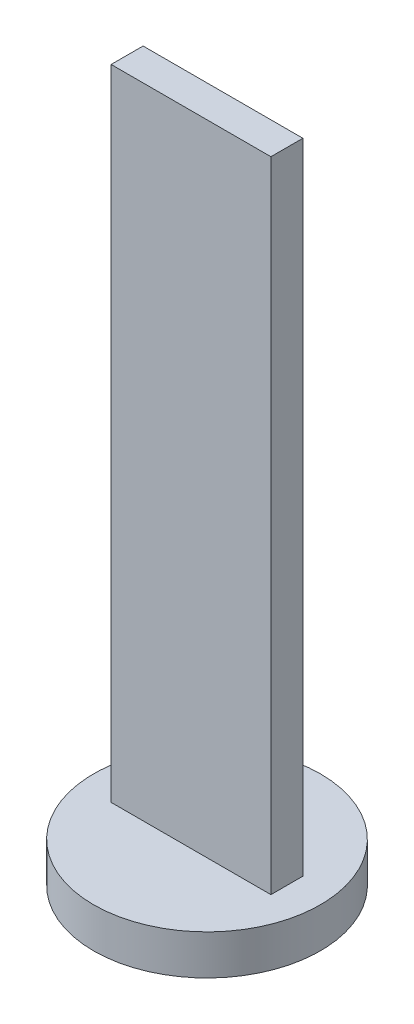
SolidWorks part; units mm, degrees
material "3.0517 (EN-AW 3003)"
ref_plane "Front Plane" through (0, 0, 0) normal (0, 0, 1) x (1, 0, 0)
ref_plane "Top Plane" through (0, 0, 0) normal (0, 1, 0) x (1, 0, 0)
ref_plane "Right Plane" through (0, 0, 0) normal (1, 0, 0) x (0, 0, -1)
sketch "Sketch1" plane through (0, 0, 0) normal (0, 0, 1) x (1, 0, 0)
  line L1 (-0.5, -2) -> (0.5, -2)
  line L2 (-0.5, -2) -> (-0.5, 2)
  line L3 (-0.5, 2) -> (0.5, 2)
  line L4 (0.5, -2) -> (0.5, 2)
  line L5 (-0.5, -2) -> (0.5, 2) construction
  line L6 (-0.5, 2) -> (0.5, -2) construction
  point P0 (0, 0)
  dimension "D1" = 4
  dimension "D2" = 1
extrude "Boss-Extrude1" add sketch "Sketch1" along normal mid plane 0.2
sketch "Sketch2" plane through (0, -2, 0) normal (0, 0, -1) x (1, 0, 0)
  line L8 (-0.75, -0.5) -> (0.75, -0.5)
  line L9 (-0.5, 0) -> (0.5, 0) construction
  line L12 (0.75, -4.25) -> (0.75, 0.25)
  line L13 (-0.75, -4.25) -> (0.75, -4.25)
  line L14 (-0.75, 0.25) -> (-0.75, -4.25)
  line L15 (0.75, 0.25) -> (-0.75, 0.25)
  line L16 (0.75, -4.25) -> (0.75, -0.5)
  line L17 (-0.75, -4.25) -> (0.75, -4.25)
  line L18 (-0.75, -0.5) -> (-0.75, -4.25)
  dimension "D1" = 0.25
  dimension "D2" = 0.5
extrude "Boss-Extrude2" [suppressed] add sketch "Sketch2" along normal mid plane 0.6
sketch "Sketch3" plane through (0, -2, 0) normal (0, -1, 0) x (1, 0, 0)
  line L0 (0.5, 0.1) -> (0.6961, 0.1392) construction
  circle A0 centre (0, 0) radius 0.7099
  dimension "D1" = 0.2
extrude "Boss-Extrude3" add sketch "Sketch3" along normal blind 0.25
